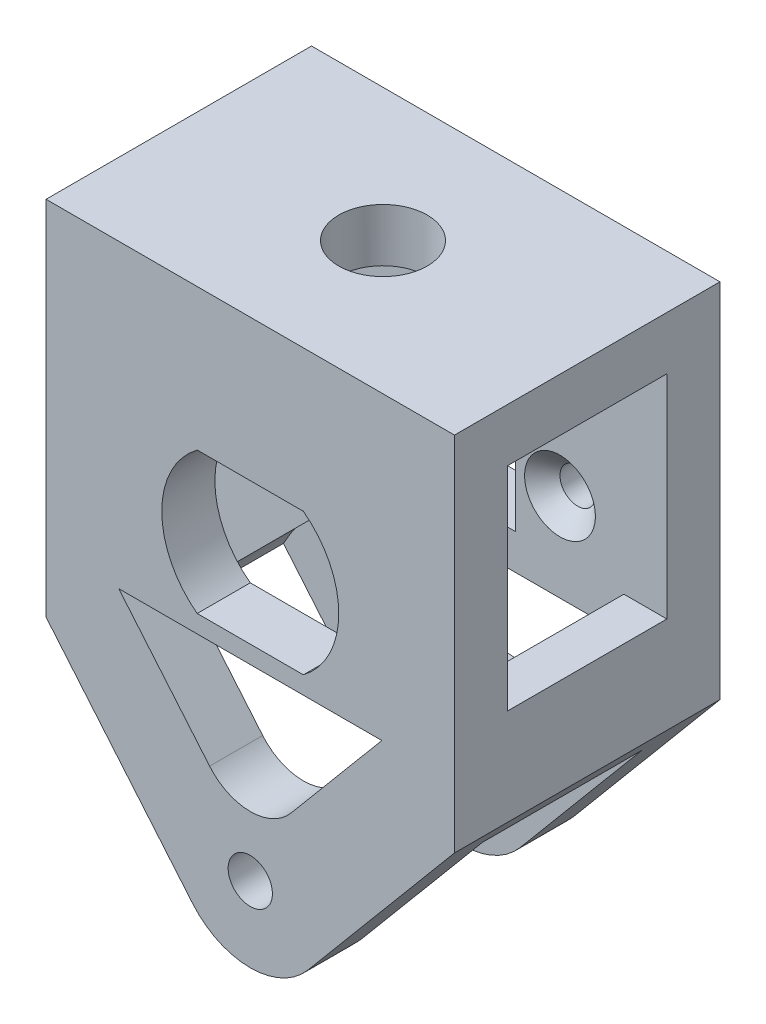
SolidWorks part; units mm, degrees
ref_plane "Front Plane" through (0, 0, 0) normal (0, 0, 1) x (1, 0, 0)
ref_plane "Top Plane" through (0, 0, 0) normal (0, 1, 0) x (1, 0, 0)
ref_plane "Right Plane" through (0, 0, 0) normal (1, 0, 0) x (0, 0, -1)
sketch "Sketch1" plane through (0, 0, 0) normal (0, 0, 1) x (1, 0, 0)
  line L0 (-16.1114, 12.589) -> (-3.2557, -2.7318)
  line L2 (3.2557, -2.7318) -> (16.1114, 12.589)
  line L3 (16.1114, 12.589) -> (9.1114, 12.589)
  line L4 (9.1114, 12.589) -> (0, 1.7304)
  line L5 (-16.1114, 12.589) -> (-9.1114, 12.589)
  line L6 (-9.1114, 12.589) -> (0, 1.7304)
  circle A0 centre (0, 0) radius 1.25
  arc A1 (-3.2557, -2.7318) -> (3.2557, -2.7318) centre (0, 0) ccw
  point P6 (0, 0)
  point P10 (0, 4.25)
  point P11 (0, 0)
  point P15 (-0.1984, 4.2454)
  dimension "D1" = 2.5
  dimension "D2" = 3
  dimension "D3" = 20
  dimension "D4" = 80
  dimension "D5" = 80
  dimension "D6" = 7
extrude "Boss-Extrude1" add sketch "Sketch1" along normal blind 3
sketch "Sketch2" plane through (0, 0, 0) normal (0, 0, 1) x (1, 0, 0)
  line L0 (16.1114, 12.589) -> (9.1114, 12.589)
  line L6 (-9.1114, 12.589) -> (-16.1114, 12.589)
  line L12 (16.1114, 12.589) -> (10.1244, 5.454)
  line L16 (6.5053, 9.4832) -> (9.1114, 12.589)
  line L17 (-9.1114, 12.589) -> (-6.5053, 9.4832)
  line L21 (-10.1244, 5.454) -> (-16.1114, 12.589)
  arc A0 (10.1244, 5.454) -> (6.5053, 9.4832) centre (0, 0) ccw
  arc A1 (-6.5053, 9.4832) -> (-10.1244, 5.454) centre (0, 0) ccw
  dimension "D3" = 23
extrude "Boss-Extrude2" add sketch "Sketch2" along normal blind 14
ref_plane "Plane1" through (0, 0, 7.5) normal (0, 0, -1) x (-1, 0, 0)
mirror "Mirror1" about plane through (0, 0, 7.5) normal (0, 0, -1) of "Boss-Extrude1"
fillet "Fillet1" radius 1 2 edges at (16.1114, 12.589, 7.5) (-16.1114, 12.589, 7.5)
fillet "Fillet3" radius 3 2 edges at (0, 1.7304, 1.5) (0, 1.7304, 13.5)
sketch "Sketch5" plane through (0, 0, 0) normal (0, 0, 1) x (1, 0, 0)
  line L0 (11.5392, 12.589) -> (11.5392, 7.14)
  line L1 (13.9669, 12.589) -> (9.1114, 12.589) construction
  line L2 (3.2557, -2.7318) -> (14.733, 10.9463) construction
  line L3 (11.5392, 7.14) -> (16.1114, 12.589)
  line L4 (16.1114, 12.589) -> (11.5392, 12.589)
  line L5 (-11.5392, 12.589) -> (-11.5392, 7.14)
  line L6 (-9.1114, 12.589) -> (-13.9669, 12.589) construction
  line L7 (-14.733, 10.9463) -> (-3.2557, -2.7318) construction
  line L8 (-11.5392, 7.14) -> (-16.1114, 12.589)
  line L9 (-16.1114, 12.589) -> (-11.5392, 12.589)
extrude "Cut-Extrude1" cut sketch "Sketch5" along normal blind 15
sketch "Sketch8" plane through (0, 0, 0) normal (0, 0, 1) x (1, 0, 0)
  line L1 (-11.5392, 12.589) -> (11.5392, 12.589)
  line L2 (-11.5392, 12.589) -> (-11.5392, 27.589)
  line L3 (-11.5392, 27.589) -> (11.5392, 27.589)
  line L4 (11.5392, 12.589) -> (11.5392, 27.589)
  point P5 (0, 0)
  dimension "D1" = 15
extrude "Boss-Extrude6" add sketch "Sketch8" along normal up to surface (15 mm away) up to face at (1.25, 0, 15)
sketch "Sketch9" plane through (0, 0, 0) normal (1, 0, 0) x (0, 0, -1)
  line L0 (-15, 27.589) -> (0, 27.589) construction
  line L1 (-12, 24.589) -> (-3, 24.589)
  line L2 (-12, 24.589) -> (-12, 12.589)
  line L3 (-12, 12.589) -> (-3, 12.589)
  line L4 (-3, 24.589) -> (-3, 12.589)
  line L5 (-12, 24.589) -> (-3, 12.589) construction
  line L6 (-12, 12.589) -> (-3, 24.589) construction
  line L7 (0, 27.589) -> (0, 7.14) construction
  line L8 (-15, 27.589) -> (-15, 7.14) construction
  point P0 (-7.5, 18.589)
  point P7 (-7.5, 27.589)
  dimension "D1" = 3
  dimension "D2" = 3
  dimension "D3" = 3
  dimension "D4" = 12
extrude "Cut-Extrude4" cut sketch "Sketch9" against normal mid plane 25
sketch "Sketch10" plane through (0, 0, 0) normal (1, 0, 0) x (0, 0, -1)
  line L0 (-15, 27.589) -> (-15, 7.14) construction
  line L1 (-12, 12.589) -> (-15, 12.589)
  line L2 (-12, 12.589) -> (-12, 10.589)
  line L3 (-12, 10.589) -> (-15, 10.589)
  line L4 (-15, 12.589) -> (-15, 10.589)
  line L5 (0, 27.589) -> (0, 7.14) construction
  line L6 (-3, 12.589) -> (0, 12.589)
  line L7 (-3, 12.589) -> (-3, 10.589)
  line L8 (-3, 10.589) -> (0, 10.589)
  line L9 (0, 12.589) -> (0, 10.589)
  dimension "D1" = 2
  dimension "D2" = 2
extrude "Boss-Extrude8" add sketch "Sketch10" along normal mid plane 23
sketch "Sketch11" plane through (0, 0, 0) normal (0, 0, 1) x (1, 0, 0)
  line L0 (7.4332, 10.589) -> (-7.4332, 10.589) construction
  line L1 (-3, 11.589) -> (3, 11.589)
  line L3 (-3, 19.589) -> (3, 19.589)
  line L5 (-3, 11.589) -> (3, 19.589) construction
  line L6 (-3, 19.589) -> (3, 11.589) construction
  arc A0 (3, 11.589) -> (3, 19.589) centre (0, 15.589) ccw
  arc A1 (-3, 19.589) -> (-3, 11.589) centre (0, 15.589) ccw
  point P8 (0, 10.589)
  point P9 (0, 0)
  dimension "D1" = 10
  dimension "D2" = 8
  dimension "D3" = 1
extrude "Cut-Extrude5" cut sketch "Sketch11" along normal up to surface (3 mm away) from surface at 12 starting at face at (0, 15.089, 12)
sketch "Sketch12" plane through (0, 0, 0) normal (0, 0, 1) x (1, 0, 0)
  line L0 (-3, 19.589) -> (3, 11.589) construction
  line L1 (5.5, 15.589) -> (-5.5, 15.589) construction
  line L2 (-3, 12.589) -> (3, 12.589)
  line L3 (-3, 12.589) -> (-3, 18.589)
  line L4 (-3, 18.589) -> (3, 18.589)
  line L5 (3, 12.589) -> (3, 18.589)
  line L6 (-3, 12.589) -> (3, 18.589) construction
  line L7 (-3, 18.589) -> (3, 12.589) construction
  circle A0 centre (5.5, 15.589) radius 1
  circle A1 centre (-5.5, 15.589) radius 1
  point P4 (0, 15.589)
  point P12 (0, 15.589)
  dimension "D4" = 2
  dimension "D1" = 6
  dimension "D2" = 6
  dimension "D3" = 11
extrude "Cut-Extrude6" cut sketch "Sketch12" along normal up to surface (3 mm away) up to face at (0, 15.089, 3)
sketch "Sketch13" plane through (0, 0, 0) normal (0, 1, 0) x (1, 0, 0)
  line L0 (-11.5392, -15) -> (11.5392, 0) construction
  circle A0 centre (0, -7.5) radius 2.5
  dimension "D1" = 5
extrude "Cut-Extrude7" cut sketch "Sketch13" against normal blind 4 from surface at 27.589 starting at face at (0, 27.589, 7.5)
chamfer "Chamfer1" distance 1 angle 45 2 edges at (-6.5, 15.589, 3) (4.5, 15.589, 3)
